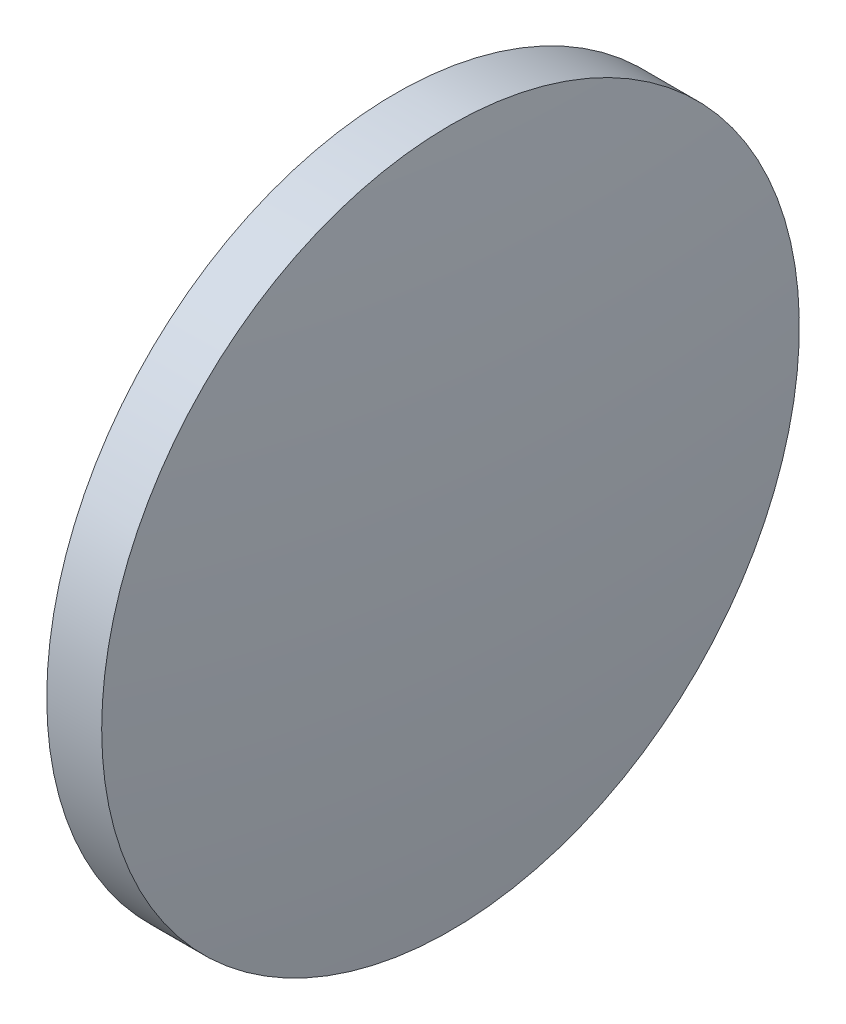
SolidWorks part; units mm, degrees
ref_plane "前视基准面" through (0, 0, 0) normal (0, 0, 1) x (1, 0, 0)
ref_plane "上视基准面" through (0, 0, 0) normal (0, 1, 0) x (1, 0, 0)
ref_plane "右视基准面" through (0, 0, 0) normal (1, 0, 0) x (0, 0, -1)
sketch "草图1" plane through (0, 0, 0) normal (0, 0, 1) x (1, 0, 0)
  line L0 (847.7384, 273.0887) -> (866.5343, 273.0887) construction
  line L1 (853.4766, 273.0887) -> (853.4766, 285.7887)
  line L2 (853.4766, 285.7887) -> (855.4766, 285.7887)
  line L3 (856.1766, 273.0887) -> (853.4766, 273.0887)
  arc A0 (856.1766, 273.0887) -> (855.4766, 285.7887) centre (740.6194, 273.0887) ccw
revolve "旋转1" add sketch "草图1" angle 360 about L0
